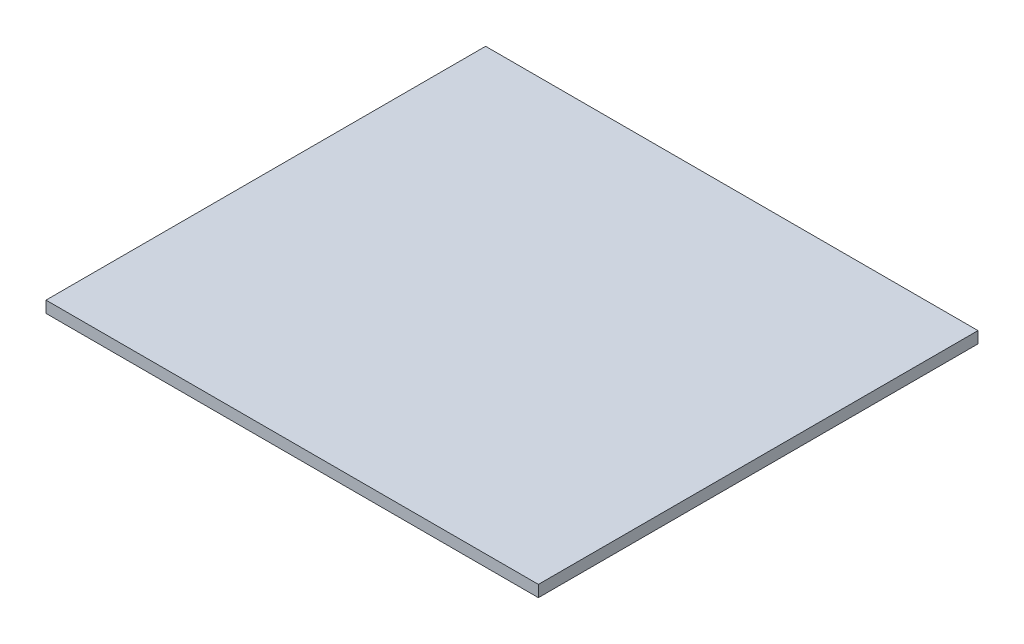
SolidWorks part; units mm, degrees
ref_plane "Front Plane" through (0, 0, 0) normal (0, 0, 1) x (1, 0, 0)
ref_plane "Top Plane" through (0, 0, 0) normal (0, 1, 0) x (1, 0, 0)
ref_plane "Right Plane" through (0, 0, 0) normal (1, 0, 0) x (0, 0, -1)
sketch "Sketch1" plane through (0, 0, 0) normal (0, 1, 0) x (1, 0, 0)
  line L1 (-29.85, 26.65) -> (29.85, 26.65)
  line L2 (-29.85, 26.65) -> (-29.85, -26.65)
  line L3 (-29.85, -26.65) -> (29.85, -26.65)
  line L4 (29.85, 26.65) -> (29.85, -26.65)
  line L5 (-29.85, 26.65) -> (29.85, -26.65) construction
  line L6 (-29.85, -26.65) -> (29.85, 26.65) construction
  point P0 (0, 0)
  dimension "D1" = 59.7
  dimension "D2" = 53.3
extrude "Extrude1" add sketch "Sketch1" along normal blind 1.4
